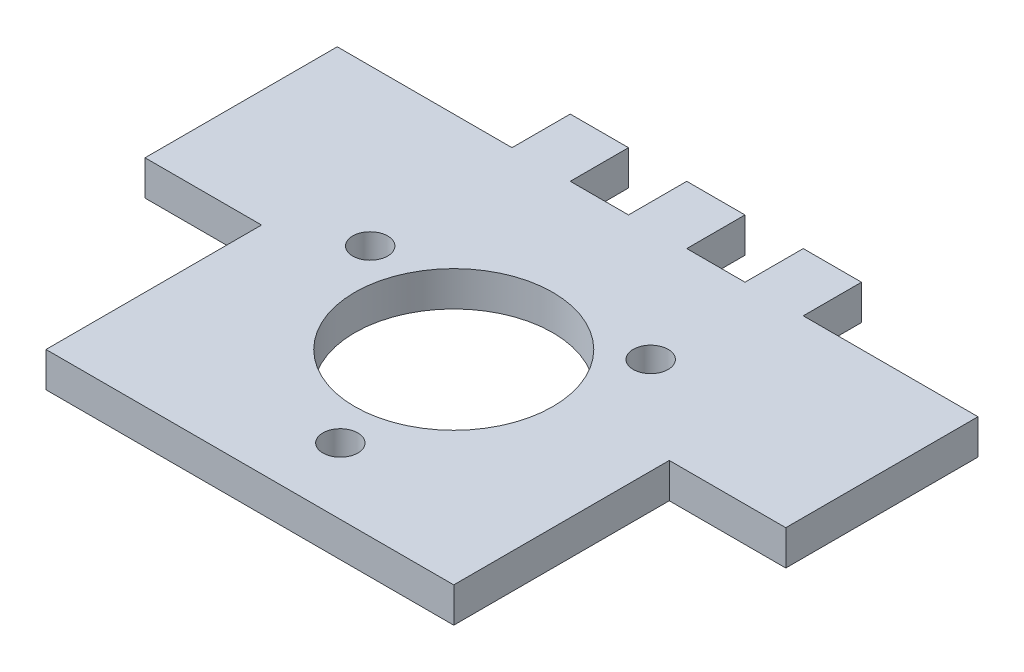
SolidWorks part; units mm, degrees
material "Balsa"
ref_plane "Plan de face" through (0, 0, 0) normal (0, 0, 1) x (1, 0, 0)
ref_plane "Plan de dessus" through (0, 0, 0) normal (0, 1, 0) x (1, 0, 0)
ref_plane "Plan de droite" through (0, 0, 0) normal (1, 0, 0) x (0, 0, -1)
sketch "Esquisse1" plane through (0, 0, 0) normal (0, 1, 0) x (1, 0, 0)
  line L1 (-17.5, 17.5) -> (17.5, 17.5)
  line L2 (-17.5, 17.5) -> (-17.5, -17.5)
  line L3 (-17.5, -17.5) -> (17.5, -17.5)
  line L4 (17.5, 17.5) -> (17.5, -17.5)
  dimension "D3" = 17.5
  dimension "D1" = 35
  dimension "D2" = 35
  dimension "D4" = 17.5
extrude "Boss.-Extru.1" add sketch "Esquisse1" along normal blind 3
sketch "Esquisse2" plane through (0, 3, 0) normal (0, 1, 0) x (1, 0, 0)
  line L1 (17.5, 17.5) -> (-17.5, 17.5) construction
  line L2 (-12.5, 17.5) -> (-7.5, 17.5)
  line L3 (-12.5, 17.5) -> (-12.5, 22.5)
  line L4 (-12.5, 22.5) -> (-7.5, 22.5)
  line L5 (-7.5, 17.5) -> (-7.5, 22.5)
  line L6 (-17.5, 17.5) -> (-17.5, -17.5) construction
  dimension "D1" = 5
  dimension "D2" = 5
  dimension "D3" = 5
extrude "Boss.-Extru.2" add sketch "Esquisse2" against normal blind 3
pattern_linear "Répétition linéaire1" count 3 spacing 10 along (1, 0, 0) of "Boss.-Extru.2"
sketch "Esquisse3" plane through (0, 3, 0) normal (0, 1, 0) x (1, 0, 0)
  line L0 (-0.6671, 3.7834) -> (3.3976, -19.269) construction
  line L1 (-17.5, 17.5) -> (-17.5, -17.5) construction
  circle A0 centre (0, 0) radius 8.5
  circle A1 centre (2.0838, -11.8177) radius 1.5
  circle A2 centre (-11.2763, 4.1042) radius 1.5
  circle A3 centre (9.1925, 7.7135) radius 1.5
  point P11 (0, 0)
  dimension "D1" = 17
  dimension "D2" = 3
  dimension "D6" = 12
  dimension "D3" = 10
  dimension "D5" = 0
  dimension "D4" = 3
extrude "Enlèv. mat.-Extru.1" cut sketch "Esquisse3" against normal blind 5
sketch "Esquisse4" plane through (0, 3, 0) normal (0, 1, 0) x (1, 0, 0)
  line L0 (-17.5, 17.5) -> (-17.5, -17.5) construction
  line L1 (-17.5, 17.5) -> (-27.5, 17.5)
  line L2 (-17.5, 17.5) -> (-17.5, 1)
  line L3 (-17.5, 1) -> (-27.5, 1)
  line L4 (-27.5, 17.5) -> (-27.5, 1)
  dimension "D1" = 1
  dimension "D2" = 16.5
  dimension "D3" = 10
extrude "Boss.-Extru.3" add sketch "Esquisse4" against normal up to surface (3 mm away) up to face at (9.1925, 0, -6.2135)
mirror "Symétrie1" about plane through (0, 0, 0) normal (1, 0, 0) of "Boss.-Extru.3"
